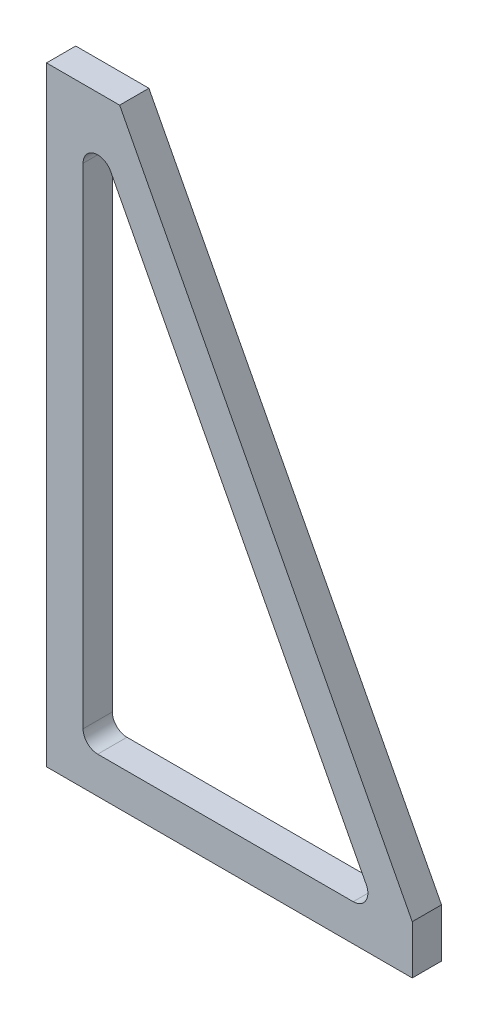
SolidWorks part; units mm, degrees
ref_plane "Front Plane" through (0, 0, 0) normal (0, 0, 1) x (1, 0, 0)
ref_plane "Top Plane" through (0, 0, 0) normal (0, 1, 0) x (1, 0, 0)
ref_plane "Right Plane" through (0, 0, 0) normal (1, 0, 0) x (0, 0, -1)
sketch "Sketch1" plane through (0, 0, 0) normal (0, 0, 1) x (1, 0, 0)
  line L0 (150, 0) -> (0, 0)
  line L1 (0, 0) -> (0, 250)
  line L2 (0, 250) -> (30, 250)
  line L3 (30, 250) -> (150, 20)
  line L4 (150, 20) -> (150, 0)
  line L5 (26.3195, 224.6265) -> (131.1114, 23.7754)
  line L7 (125.7919, 15) -> (21, 15)
  line L8 (15, 21) -> (15, 221.8511)
  line L10 (135, 15) -> (15, 15) construction
  line L12 (20.9072, 235) -> (135, 16.3222) construction
  line L13 (15, 235) -> (20.9072, 235) construction
  line L14 (15, 15) -> (15, 235) construction
  line L15 (135, 16.3222) -> (135, 15) construction
  arc A0 (26.3195, 224.6265) -> (15, 221.8511) centre (21, 221.8511) ccw
  arc A1 (21, 15) -> (15, 21) centre (21, 21) cw
  arc A2 (131.1114, 23.7754) -> (125.7919, 15) centre (125.7919, 21) cw
  dimension "D6" = 6
  dimension "D7" = 6
  dimension "D8" = 6
  dimension "D1" = 20
  dimension "D2" = 30
  dimension "D3" = 250
  dimension "D4" = 150
  dimension "D5" = 15
extrude "Boss-Extrude1" add sketch "Sketch1" along normal blind 12
